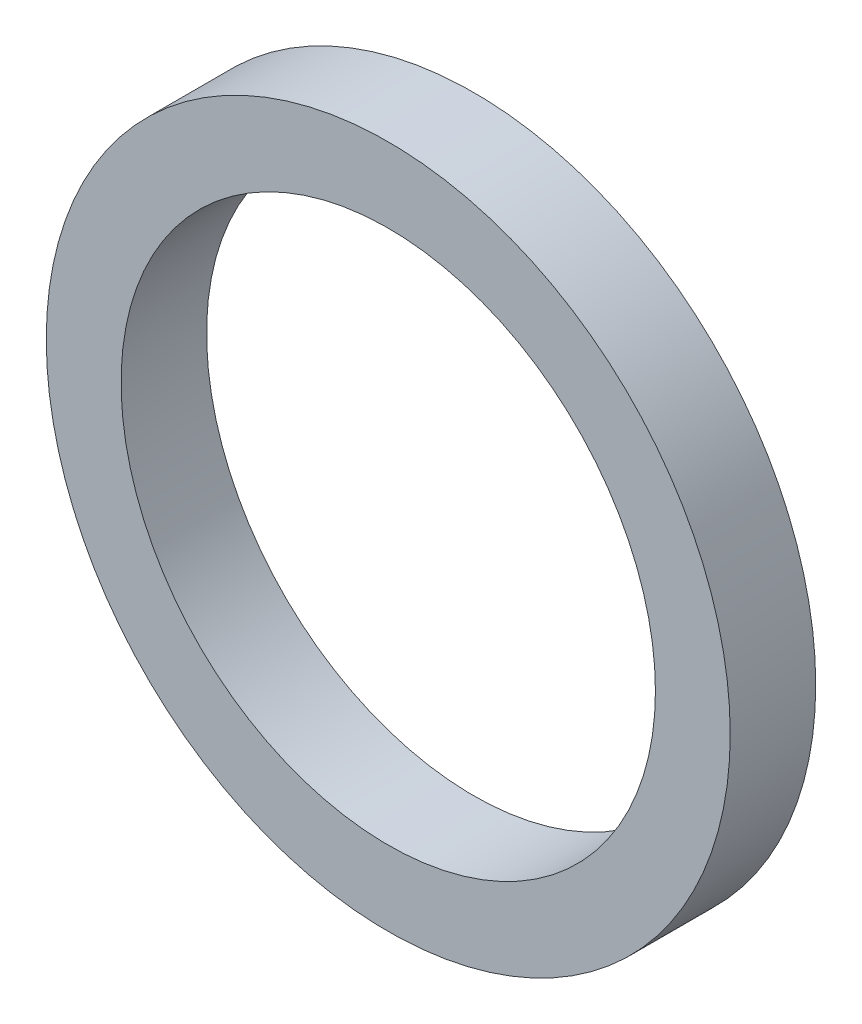
SolidWorks part; units mm, degrees
ref_plane "前视基准面" through (0, 0, 0) normal (0, 0, 1) x (1, 0, 0)
ref_plane "上视基准面" through (0, 0, 0) normal (0, 1, 0) x (1, 0, 0)
ref_plane "右视基准面" through (0, 0, 0) normal (1, 0, 0) x (0, 0, -1)
sketch "草图1" plane through (0, 0, 0) normal (0, 0, 1) x (1, 0, 0)
  circle A0 centre (0, 0) radius 12.5
  circle A1 centre (0, 0) radius 16
extrude "凸台-拉伸1" add sketch "草图1" along normal blind 4
